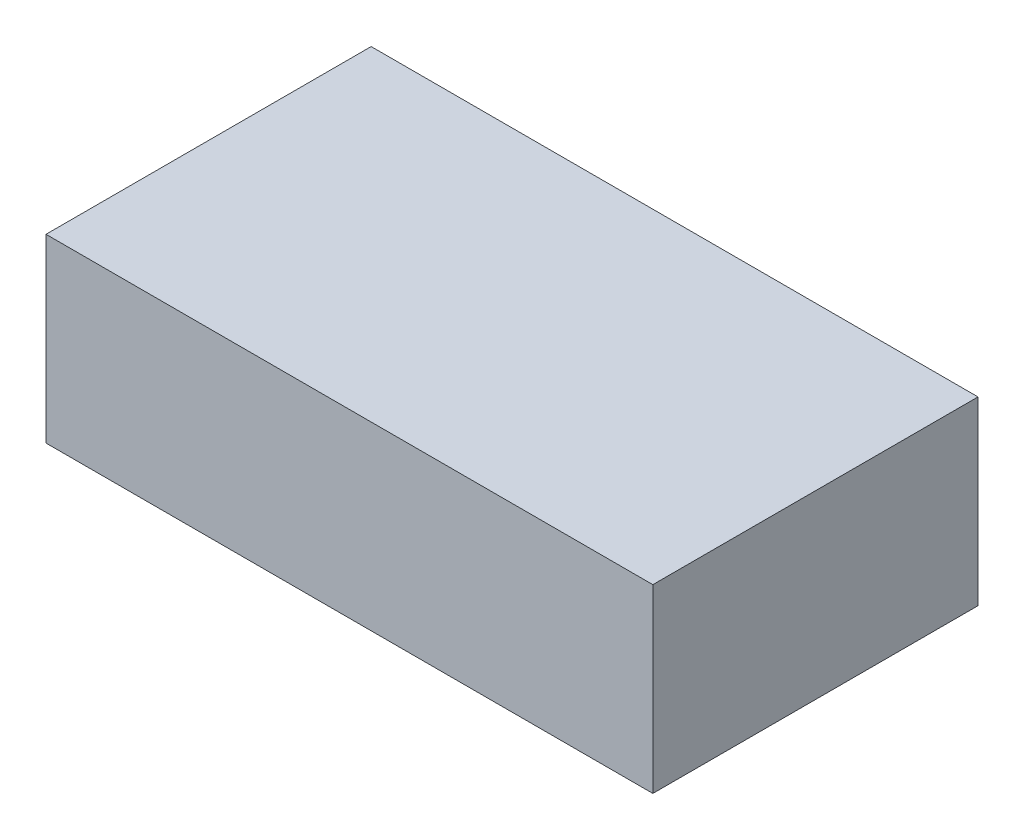
SolidWorks part; units mm, degrees
ref_plane "Front Plane" through (0, 0, 0) normal (0, 0, 1) x (1, 0, 0)
ref_plane "Top Plane" through (0, 0, 0) normal (0, 1, 0) x (1, 0, 0)
ref_plane "Right Plane" through (0, 0, 0) normal (1, 0, 0) x (0, 0, -1)
sketch "Sketch1" plane through (0, 0, 0) normal (0, 1, 0) x (1, 0, 0)
  line L1 (0, 0) -> (30.9, 0)
  line L2 (0, 0) -> (0, 14.7)
  line L3 (0, 14.7) -> (30.9, 14.7)
  line L4 (30.9, 0) -> (30.9, 14.7)
  dimension "D1" = 30.9
  dimension "D2" = 14.7
extrude "Boss-Extrude1" add sketch "Sketch1" along normal blind 2
sketch "Sketch2" plane through (0, 2, 0) normal (0, 1, 0) x (1, 0, 0)
  line L0 (30.9, 0) -> (30.9, 14.7) construction
  line L1 (0, 0) -> (30.9, 0)
  line L2 (0, 0) -> (0, -2)
  line L3 (0, -2) -> (30.9, -2)
  line L4 (30.9, 0) -> (30.9, -2)
  line L6 (0, 14.7) -> (30.9, 14.7)
  line L7 (0, 14.7) -> (0, 16.7)
  line L8 (0, 16.7) -> (30.9, 16.7)
  line L9 (30.9, 14.7) -> (30.9, 16.7)
  line L10 (30.9, 16.7) -> (32.9, 16.7)
  line L11 (30.9, 16.7) -> (30.9, -2)
  line L12 (30.9, -2) -> (32.9, -2)
  line L13 (32.9, 16.7) -> (32.9, -2)
  line L14 (0, 16.7) -> (-2, 16.7)
  line L15 (0, 16.7) -> (0, -2)
  line L16 (0, -2) -> (-2, -2)
  line L17 (-2, 16.7) -> (-2, -2)
  point P15 (0, 0)
  line M11 (0, 14.7) -> (0, 0)
  line M12 (0, 0) -> (30.9, 0)
  line M13 (30.9, 0) -> (30.9, 14.7)
  line M14 (30.9, 14.7) -> (0, 14.7)
  dimension "D1" = 2
  dimension "D2" = 2
  dimension "D3" = 2
  dimension "D4" = 2
extrude "Boss-Extrude2" add sketch "Sketch2" against normal blind 10.4 contours L14 L17 L16 L2 L7 M11 | L9 L8 L7 M14 | L4 L2 L3 M12 | L13 L10 L9 L4 L12 M13
